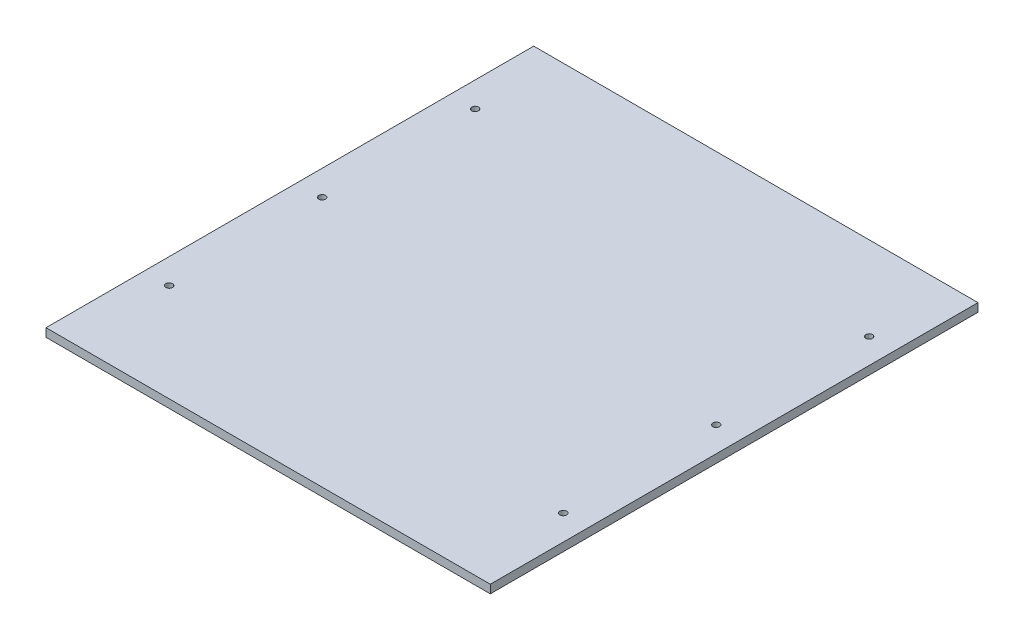
SolidWorks part; units mm, degrees
ref_plane "Front Plane" through (0, 0, 0) normal (0, 0, 1) x (1, 0, 0)
ref_plane "Top Plane" through (0, 0, 0) normal (0, 1, 0) x (1, 0, 0)
ref_plane "Right Plane" through (0, 0, 0) normal (1, 0, 0) x (0, 0, -1)
sketch "Sketch1" plane through (0, 0, 0) normal (0, 1, 0) x (1, 0, 0)
  line L1 (-139.6047, 141.3176) -> (125.6753, 141.3176)
  line L2 (-139.6047, 141.3176) -> (-139.6047, -149.8824)
  line L3 (-139.6047, -149.8824) -> (125.6753, -149.8824)
  line L4 (125.6753, 141.3176) -> (125.6753, -149.8824)
  dimension "D1" = 291.2
  dimension "D2" = 265.28
extrude "Boss-Extrude1" add sketch "Sketch1" along normal blind 5
sketch "Sketch3" plane through (0, 5, 0) normal (0, 1, 0) x (1, 0, 0)
  line L0 (-124.6047, 190.2175) -> (-124.6047, -190.2175) construction
  line L1 (-139.6047, 141.3176) -> (-139.6047, -149.8824) construction
  line L2 (0, 237.5492) -> (0, -200.2691) construction
  line L3 (-182.3213, 0) -> (228.7542, 0) construction
  line L4 (125.6753, 141.3176) -> (-139.6047, 141.3176) construction
  line L5 (110.6753, 169.4131) -> (110.6753, -185.0661) construction
  line L6 (125.6753, -149.8824) -> (125.6753, 141.3176) construction
  circle A0 centre (-124.6047, 91.3176) radius 2
  circle A1 centre (-124.6047, 0) radius 2
  circle A2 centre (-124.6047, -91.3176) radius 2
  circle A3 centre (110.6753, 91.3176) radius 2
  circle A4 centre (110.6753, 0) radius 2
  circle A5 centre (110.6753, -91.3176) radius 2
  dimension "D3" = 4
  dimension "D1" = 15
  dimension "D2" = 50
  dimension "D4" = 15
extrude "Cut-Extrude1" cut sketch "Sketch3" against normal blind 5
